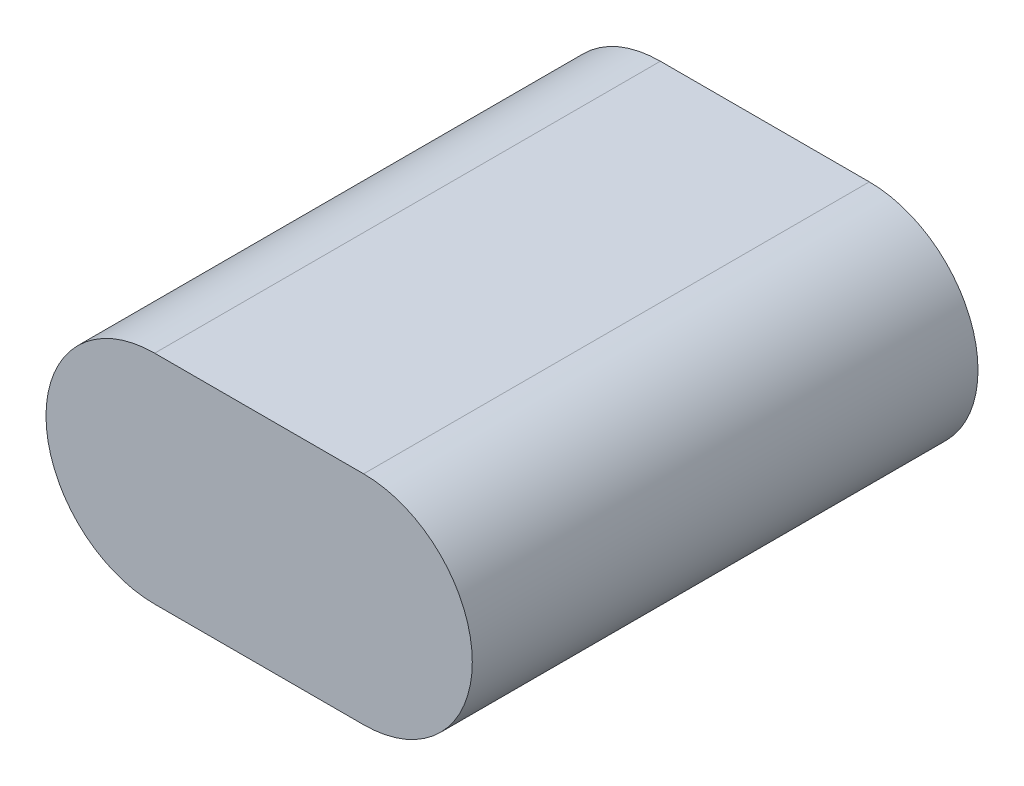
SolidWorks part; units mm, degrees
ref_plane "前视基准面" through (0, 0, 0) normal (0, 0, 1) x (1, 0, 0)
ref_plane "上视基准面" through (0, 0, 0) normal (0, 1, 0) x (1, 0, 0)
ref_plane "右视基准面" through (0, 0, 0) normal (1, 0, 0) x (0, 0, -1)
sketch "草图1" plane through (0, 0, 0) normal (0, 0, 1) x (1, 0, 0)
  line L1 (-50, 52) -> (50, 52)
  line L2 (-50, -52) -> (50, -52)
  arc A1 (-50, 52) -> (-50, -52) centre (-50, 0) ccw
  arc A2 (50, 52) -> (50, -52) centre (50, 0) cw
  point P11 (0, -52)
extrude "凸台-拉伸1" add sketch "草图1" along normal blind 242
sketch3d "3D草图1"
  line L0 (0, 52, 242) -> (0, -52, 242) construction
  line L1 (50, 52, 242) -> (-50, 52, 242) construction
  line L2 (-50, -52, 242) -> (50, -52, 242) construction
  line L3 (0, -52, 0) -> (0, 52, 0) construction
  line L4 (-50, -52, 0) -> (50, -52, 0) construction
  line L5 (50, 52, 0) -> (-50, 52, 0) construction
  line L6 (0, 0, 242) -> (0, 0, 0) construction
ref_point "点1"
